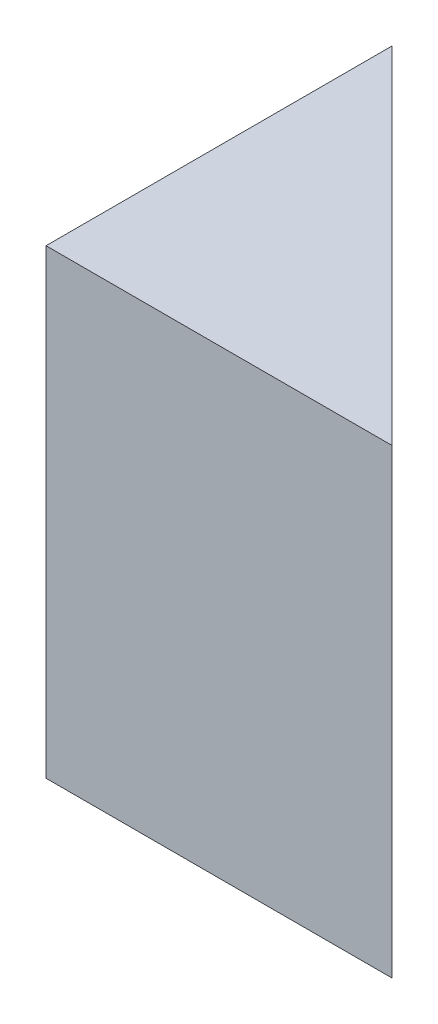
SolidWorks part; units mm, degrees
ref_plane "Front Plane" through (0, 0, 0) normal (0, 0, 1) x (1, 0, 0)
ref_plane "Top Plane" through (0, 0, 0) normal (0, 1, 0) x (1, 0, 0)
ref_plane "Right Plane" through (0, 0, 0) normal (1, 0, 0) x (0, 0, -1)
sketch "Sketch1" plane through (0, 0, 0) normal (0, 1, 0) x (1, 0, 0)
  line L0 (0, 19.05) -> (0, 0)
  line L1 (0, 0) -> (19.05, 0)
  line L2 (19.05, 0) -> (0, 19.05)
  dimension "D1" = 19.05
extrude "Boss-Extrude1" add sketch "Sketch1" along normal blind 25.4
